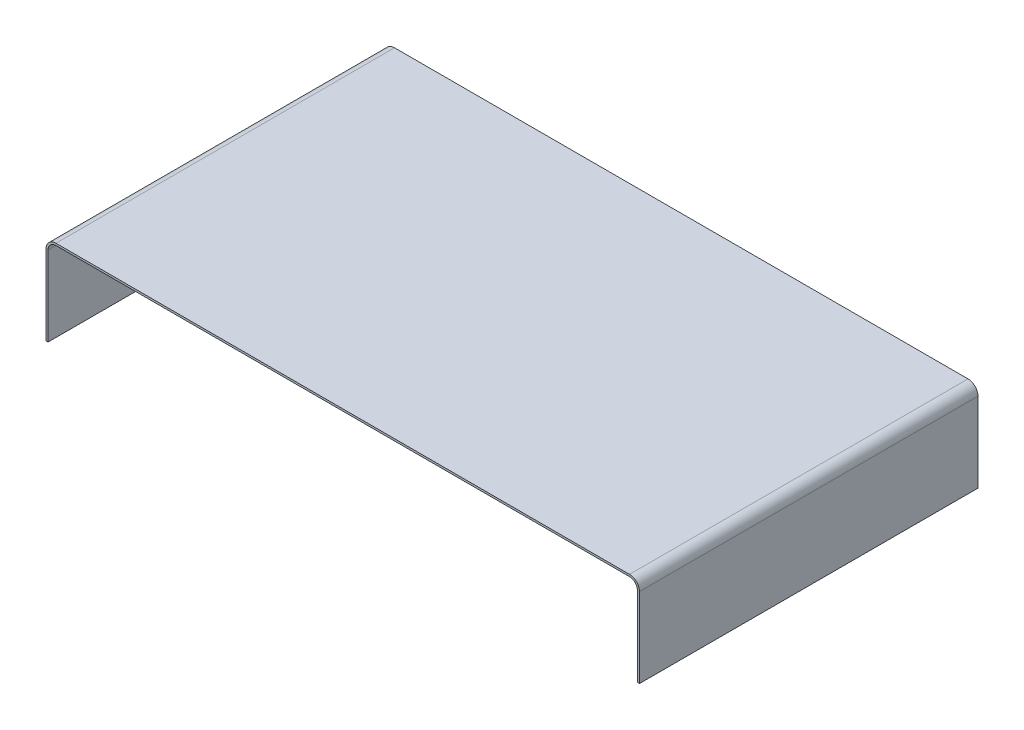
SolidWorks part; units mm, degrees
ref_plane "Plano frontal" through (0, 0, 0) normal (0, 0, 1) x (1, 0, 0)
ref_plane "Plano superior" through (0, 0, 0) normal (0, 1, 0) x (1, 0, 0)
ref_plane "Plano direito" through (0, 0, 0) normal (1, 0, 0) x (0, 0, -1)
sketch "Esboço1" plane through (0, 0, 0) normal (0, 0, 1) x (1, 0, 0)
  line L0 (0, 0) -> (0, 40)
  line L1 (298, 0) -> (298, 40)
  line L2 (293, 45) -> (5, 45)
  line L3 (297, 0) -> (297, 40)
  line L4 (293, 44) -> (5, 44)
  line L5 (1, 0) -> (1, 40)
  line L6 (0, 0) -> (1, 0)
  line L7 (297, 0) -> (298, 0)
  arc A0 (293, 45) -> (298, 40) centre (293, 40) cw
  arc A1 (5, 45) -> (0, 40) centre (5, 40) ccw
  arc A2 (293, 44) -> (297, 40) centre (293, 40) cw
  arc A3 (5, 44) -> (1, 40) centre (5, 40) ccw
  point P7 (298, 45)
  point P10 (0, 45)
  dimension "D3" = 5
  dimension "D1" = 45
  dimension "D2" = 298
extrude "Ressalto-extrusão1" add sketch "Esboço1" along normal blind 170
